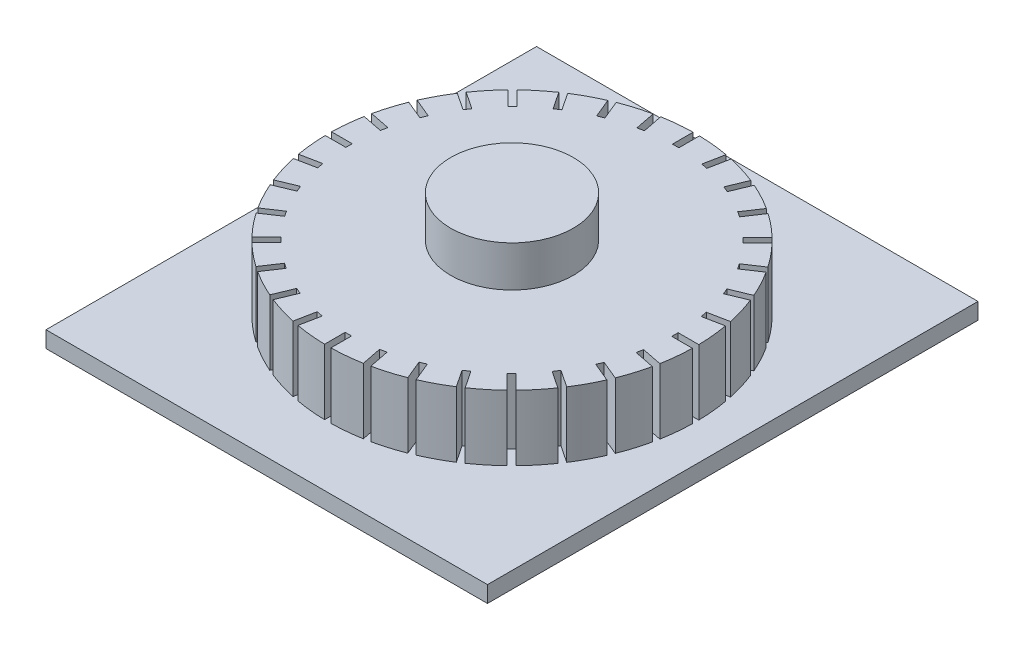
SolidWorks part; units mm, degrees
material "Zinc AC43A (Zn-4Al-2.5Cu-0.04Mg; Number 2 Die Casting Alloy; Zamak 2), Die Cast"
ref_plane "Front Plane" through (0, 0, 0) normal (0, 0, 1) x (1, 0, 0)
ref_plane "Top Plane" through (0, 0, 0) normal (0, 1, 0) x (1, 0, 0)
ref_plane "Right Plane" through (0, 0, 0) normal (1, 0, 0) x (0, 0, -1)
sketch "Sketch1" plane through (0, 0, 0) normal (0, 1, 0) x (1, 0, 0)
  line L1 (-270, -300) -> (270, -300)
  line L2 (-270, -300) -> (-270, 300)
  line L3 (-270, 300) -> (270, 300)
  line L4 (270, -300) -> (270, 300)
  line L5 (-270, -300) -> (270, 300) construction
  line L6 (-270, 300) -> (270, -300) construction
  point P0 (0, 0)
  dimension "D1" = 540
  dimension "D2" = 600
extrude "Boss-Extrude1" add sketch "Sketch1" along normal blind 20
sketch "Sketch2" plane through (0, 20, 0) normal (0, 1, 0) x (1, 0, 0)
  circle A0 centre (0, 0) radius 225
  dimension "D1" = 450
extrude "Boss-Extrude2" add sketch "Sketch2" along normal blind 80
sketch "Sketch3" plane through (0, 100, 0) normal (0, 1, 0) x (1, 0, 0)
  circle A0 centre (0, 0) radius 75
  dimension "D1" = 150
extrude "Boss-Extrude3" add sketch "Sketch3" along normal blind 50
sketch "Sketch4" plane through (0, 100, 0) normal (0, 1, 0) x (1, 0, 0)
  line L5 (-4.327, -199.7675) -> (3.4816, -199.7675)
  line L6 (-4.327, -199.7675) -> (-4.327, -230.1786)
  line L7 (-4.327, -230.1786) -> (3.4816, -230.1786)
  line L8 (3.4816, -199.7675) -> (3.4816, -230.1786)
  line L9 (-4.327, -199.7675) -> (3.4816, -230.1786) construction
  line L10 (-4.327, -230.1786) -> (3.4816, -199.7675) construction
  point P0 (-0.4227, -214.973)
  point P1 (-0.4227, -214.973)
extrude "Cut-Extrude2" cut sketch "Sketch4" against normal up to surface (80 mm away) up to face at (0, 20, 225)
pattern_circular "CirPattern1" count 32 over 360 about axis through (0, 0, 0) along (0, 1, 0) of "Cut-Extrude2"
